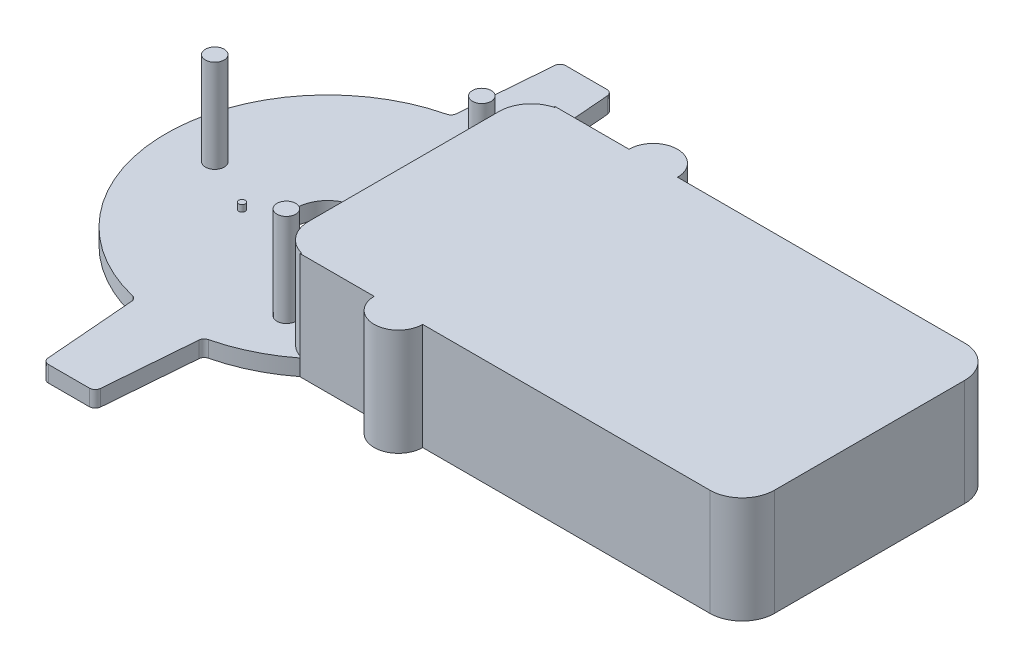
SolidWorks part; units mm, degrees
material "ABS"
ref_plane "Front Plane" through (0, 0, 0) normal (0, 0, 1) x (1, 0, 0)
ref_plane "Top Plane" through (0, 0, 0) normal (0, 1, 0) x (1, 0, 0)
ref_plane "Right Plane" through (0, 0, 0) normal (1, 0, 0) x (0, 0, -1)
sketch "Sketch1" plane through (0, 0, 0) normal (0, 1, 0) x (1, 0, 0)
  line L0 (68.7838, -39.4) -> (157.5838, -39.4)
  line L1 (53.7838, -39.4) -> (30.7838, -39.4)
  line L2 (167.5838, -29.4) -> (167.5838, 29.4)
  line L3 (-50, 0) -> (167.5838, 0)
  line L4 (-119.6711, 0) -> (119.6711, 0) construction
  line L7 (0, -50) -> (0, -80)
  line L8 (0, -71.5) -> (0, 71.5) construction
  line L9 (-6.3504, -80) -> (6.3504, -80)
  line L10 (-8.1321, -78.3557) -> (-10.395, -50.1924)
  line L11 (10.4104, -50) -> (10.5, -50)
  line L12 (8.1321, 78.3557) -> (10.395, 50.1924)
  line L13 (10.4104, 50) -> (10.5, 50)
  line L14 (8.1321, -78.3557) -> (10.395, -50.1924)
  line L15 (-8.1321, 78.3557) -> (-10.395, 50.1924)
  line L16 (-6.3504, 80) -> (6.3504, 80)
  line L17 (0, 50) -> (0, 80)
  line L18 (53.7838, 39.4) -> (30.7838, 39.4)
  line L19 (68.7838, 39.4) -> (157.5838, 39.4)
  arc A0 (157.5838, -39.4) -> (167.5838, -29.4) centre (157.5838, -29.4) ccw
  arc A1 (53.7838, -39.4) -> (68.7838, -39.4) centre (61.2838, -39.4) ccw
  arc A2 (-11.7564, 48.5982) -> (-11.7564, -48.5982) centre (0, 0) ccw
  arc A5 (11.7564, -48.5982) -> (30.7838, -39.4) centre (0, 0) ccw
  arc A6 (11.7564, -48.5982) -> (10.395, -50.1924) centre (12.1767, -50.3356) ccw
  arc A7 (8.1321, -78.3557) -> (6.3504, -80) centre (6.3504, -78.2125) cw
  arc A8 (-6.3504, -80) -> (-8.1321, -78.3557) centre (-6.3504, -78.2125) cw
  arc A9 (-10.395, -50.1924) -> (-11.7564, -48.5982) centre (-12.1767, -50.3356) ccw
  arc A10 (-10.395, 50.1924) -> (-11.7564, 48.5982) centre (-12.1767, 50.3356) cw
  arc A11 (-6.3504, 80) -> (-8.1321, 78.3557) centre (-6.3504, 78.2125) ccw
  arc A12 (8.1321, 78.3557) -> (6.3504, 80) centre (6.3504, 78.2125) ccw
  arc A13 (11.7564, 48.5982) -> (10.395, 50.1924) centre (12.1767, 50.3356) cw
  arc A14 (11.7564, 48.5982) -> (30.7838, 39.4) centre (0, 0) cw
  arc A15 (53.7838, 39.4) -> (68.7838, 39.4) centre (61.2838, 39.4) cw
  arc A16 (157.5838, 39.4) -> (167.5838, 29.4) centre (157.5838, 29.4) cw
  point P32 (10.5, -48.8851)
  point P36 (8, -80)
  point P39 (-8, -80)
  point P42 (-10.5, -48.8851)
  point P59 (-10.5, 48.8851)
  point P60 (-8, 80)
  point P61 (8, 80)
  point P62 (10.5, 48.8851)
  dimension "D1" = 20
  dimension "D9" = 100
  dimension "D10" = 1.7875
  dimension "D2" = 10
  dimension "D4" = 88.8
  dimension "D6" = 0
  dimension "D7" = 7.5
  dimension "D8" = 23
  dimension "D11" = 39.4
  dimension "D3" = 80
  dimension "D5" = 8
  dimension "D12" = 10.5
extrude "Boss-Extrude2" add sketch "Sketch1" along normal blind 33
sketch "Sketch2" plane through (0, 33, 0) normal (0, 1, 0) x (1, 0, 0)
  line L0 (53.7838, 39.4) -> (30.7838, 39.4) construction
  line L1 (167.5838, -29.4) -> (167.5838, 29.4) construction
  line L2 (23.5838, 29.4) -> (23.5838, -29.4)
  line L3 (-18.15, 0) -> (18.15, 0) construction
  line L4 (0, -18.15) -> (0, 18.15) construction
  line L5 (13.4723, 85.2506) -> (-13.4723, 85.2506)
  line L6 (13.4723, 85.2506) -> (13.4723, 48.1508)
  line L8 (-13.4723, 85.2506) -> (-13.4723, 48.1508)
  line L9 (13.4723, 85.2506) -> (0, 65.7311) construction
  line L10 (11.8389, 48.5782) -> (-13.4723, 85.2506) construction
  line L12 (-13.4723, -85.2506) -> (-13.4723, -48.1508)
  line L13 (13.4723, -85.2506) -> (-13.4723, -85.2506)
  line L14 (13.4723, -85.2506) -> (13.4723, -48.1508)
  line L15 (0, -65.7311) -> (-13.4723, -85.2506) construction
  line L16 (13.4723, -85.2506) -> (-11.8389, -48.5782) construction
  arc A0 (31.1612, 39.1021) -> (13.4723, 48.1508) centre (0, 0) ccw
  arc A1 (31.1612, 39.1021) -> (23.5838, 29.4) centre (33.5838, 29.4) ccw
  arc A2 (31.1612, -39.1021) -> (23.5838, -29.4) centre (33.5838, -29.4) cw
  arc A3 (13.4723, -48.1508) -> (31.1612, -39.1021) centre (0, 0) ccw
  arc A4 (-13.4723, 48.1508) -> (-13.4723, -48.1508) centre (0, 0) ccw
  point P1 (0, 65.7311)
  point P14 (23.5838, 0)
  point P26 (0, -65.7311)
  dimension "D1" = 100
  dimension "D2" = 20
  dimension "D3" = 144
  dimension "D4" = 0
extrude "Cut-Extrude1" cut sketch "Sketch2" against normal blind 28
sketch "Sketch3" plane through (0, 5, 0) normal (0, 1, 0) x (1, 0, 0)
  circle A0 centre (0, 0) radius 10
  dimension "D1" = 20
extrude "Cut-Extrude2" cut sketch "Sketch3" against normal through all
sketch "Sketch5" plane through (0, 5, 0) normal (0, 1, 0) x (1, 0, 0)
  circle A0 centre (-34.9, 0) radius 2.9
  arc A10 (-11.7564, 48.5982) -> (-11.7564, -48.5982) centre (0, 0) ccw construction
  dimension "D1" = 5.8
  dimension "D2" = 15.1
  dimension "D3" = 0
extrude "Boss-Extrude3" add sketch "Sketch5" along normal blind 28.7
pattern_circular "CirPattern1" count 3 over 360 about axis through (0, 0, 0) along (0, 1, 0) of "Boss-Extrude3"
sketch "Sketch6" plane through (0, 5, 0) normal (0, 1, 0) x (1, 0, 0)
  line L0 (23.5838, -29.4) -> (23.5838, 29.4) construction
  circle A0 centre (-17.8962, -8.5876) radius 1
  point P2 (0, 0)
  dimension "D1" = 2
  dimension "D2" = 19.85
  dimension "D3" = 41.48
extrude "Boss-Extrude4" add sketch "Sketch6" along normal blind 2
equation "\"D12@Sketch1\"=0.021/2"
equation "\"D2@Sketch5\"=0.018 - \"D1@Sketch5\"/2"
equation "\"D3@Sketch6\"=0.04348m - \"D1@Sketch6\""
